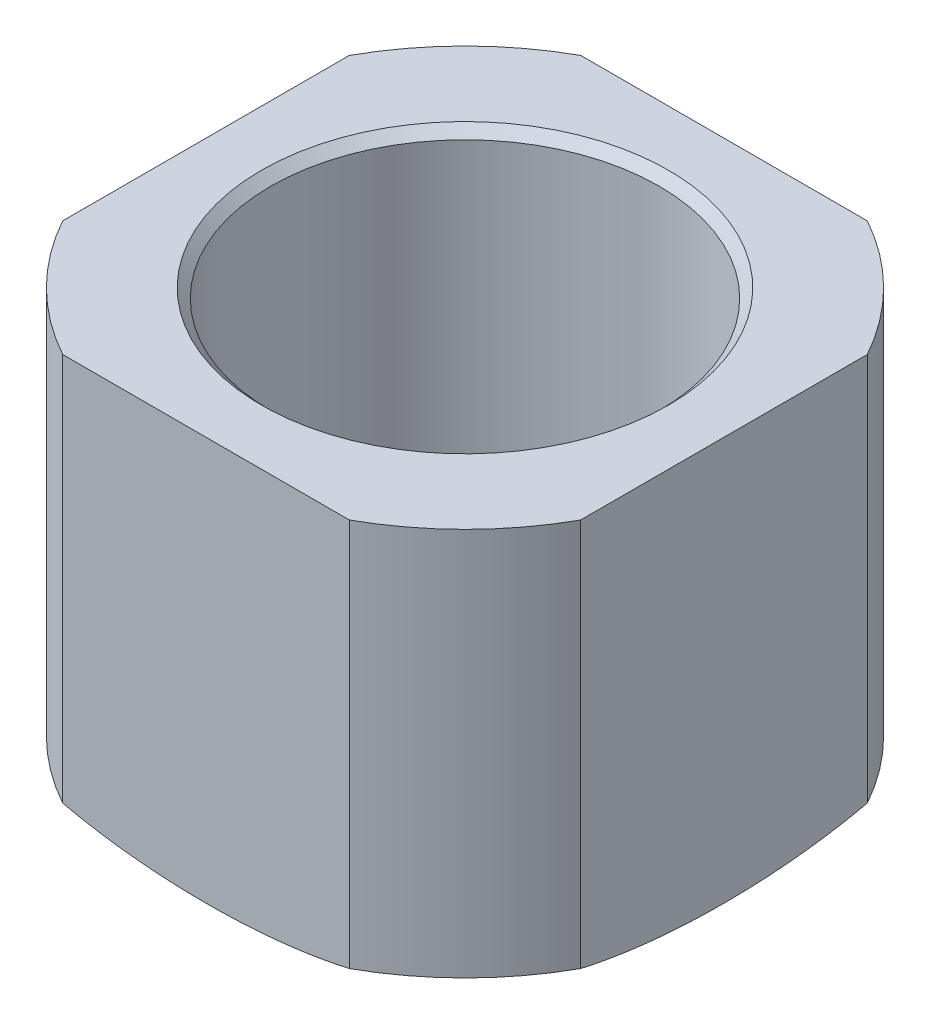
SolidWorks part; units mm, degrees
material "Plain Carbon Steel"
ref_plane "Front Plane" through (0, 0, 0) normal (0, 0, 1) x (1, 0, 0)
ref_plane "Top Plane" through (0, 0, 0) normal (0, 1, 0) x (1, 0, 0)
ref_plane "Right Plane" through (0, 0, 0) normal (1, 0, 0) x (0, 0, -1)
sketch "Sketch1" plane through (0, 0, 0) normal (0, 0, 1) x (1, 0, 0)
  line L0 (0, 0) -> (25.4, 0) construction
  line L1 (25.4, 0) -> (25.4, 36.5125) construction
  line L2 (25.4, 36.5125) -> (16.6687, 36.5125)
  line L3 (16.6687, 36.5125) -> (16.6687, 7.3619)
  line L5 (0, 53.4636) -> (0, 0) construction
  line L6 (25.4, 36.5125) -> (25.4, 3.175)
  line L10 (0, 53.4636) -> (0, 0) construction
  line L11 (11.1125, 3.175) -> (11.1125, 0)
  line L12 (11.1125, 3.175) -> (16.6687, 7.3619)
  arc A3 (11.1125, 0) -> (25.4, 3.175) centre (11.1125, 33.7344) ccw
  dimension "D1" = 25.4
  dimension "D2" = 33.3375
  dimension "D3" = 37
  dimension "D4" = 16.6687
  dimension "D5" = 11.1125
  dimension "D6" = 3.175
revolve "Revolve1" add sketch "Sketch1" angle 360 about L5
chamfer "Chamfer1" distance 0.7937 angle 45 1 edges at (-16.6687, 36.5125, 0)
thread "Thread1" pitch 2.1167 start angle 0, offset 0.3969, length 19.8438, pitch 2.1167, diameter 33.3375
ref_plane "Plane2" through (-16.6687, 36.1156, 0) normal (0, 0, 1) x (-1, 0, 0)
sketch "Thread Profile2" plane through (-16.6687, 36.1156, 0) normal (0, 0, 1) x (-1, 0, 0)
  line L0 (0, 0) -> (0, 2.1167) construction
  line L11 (0, 0) -> (0, 1.8521)
  line L12 (0, 1.8521) -> (-1.1457, 1.1906)
  line L13 (-1.1457, 1.1906) -> (-1.1457, 0.6615)
  line L15 (-1.1457, 0.6615) -> (0, 0)
  line L17 (-1.1457, 0.926) -> (0, 0.926) construction
  point P2 (0, 0)
  dimension "Pitch" = 2.1167
  dimension "Profile_Angle" = 60
  dimension "Profile_Land" = 0.5292
  dimension "Profile_Height" = 1.1457
sketch "Sketch7" plane through (0, 0, 0) normal (0, 1, 0) x (1, 0, 0)
  circle A0 centre (0, 0) radius 11.1125
  ellipse E0 centre (0, 0) end of major axis (-11.1125, 0) minor radius 9.525 construction
  dimension "D1" = 22.225
  dimension "D2" = 19.05
sketch "Sketch8" plane through (0, 36.5125, 0) normal (0, 1, 0) x (1, 0, 0)
  line L0 (-22.225, 12.2967) -> (-22.225, -12.2967)
  circle A0 centre (0, 0) radius 25.4 construction
  arc A1 (-22.225, -12.2967) -> (-22.225, 12.2967) centre (0, 0) cw
  point P5 (-22.225, 0)
  point P6 (-25.4, 0)
  dimension "D1" = 3.175
extrude "Cut-Extrude1" cut sketch "Sketch8" against normal through all
pattern_circular "CirPattern1" count 4 every 90 about axis through (0, 0, 0) along (0, 1, 0) of "Cut-Extrude1"
